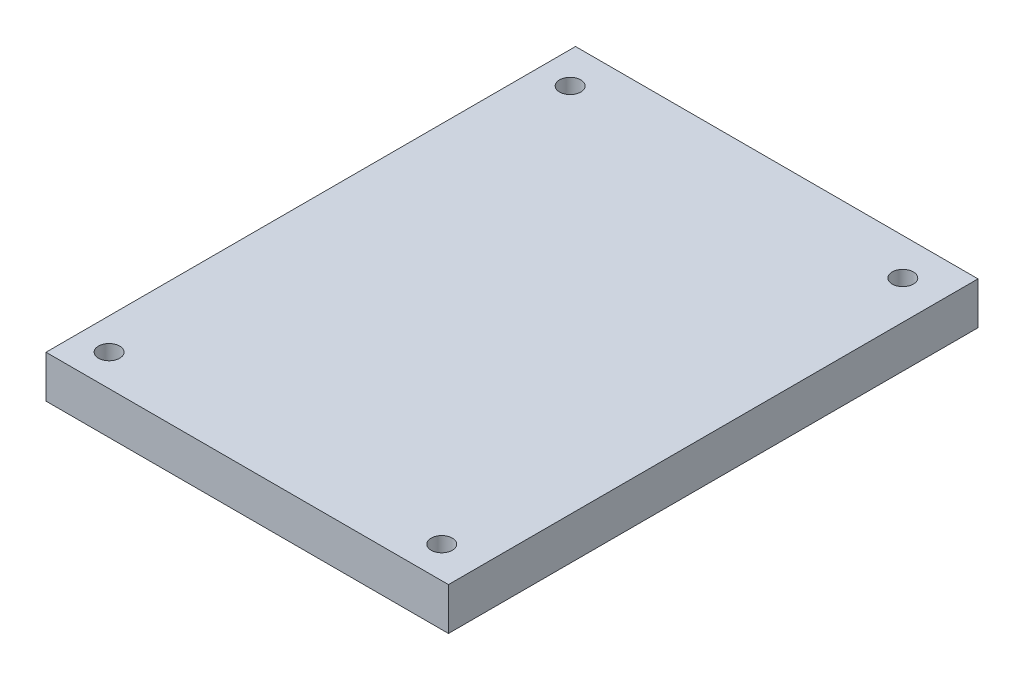
SolidWorks part; units mm, degrees
ref_plane "Ön Düzlem" through (0, 0, 0) normal (0, 0, 1) x (1, 0, 0)
ref_plane "Üst Düzlem" through (0, 0, 0) normal (0, 1, 0) x (1, 0, 0)
ref_plane "Sağ Düzlem" through (0, 0, 0) normal (1, 0, 0) x (0, 0, -1)
sketch "Çizim1" plane through (0, 0, 0) normal (0, 1, 0) x (1, 0, 0)
  line L1 (-7.4468, -9.641) -> (11.5532, -9.641)
  line L2 (-7.4468, -9.641) -> (-7.4468, 15.359)
  line L3 (-7.4468, 15.359) -> (11.5532, 15.359)
  line L4 (11.5532, -9.641) -> (11.5532, 15.359)
  circle A0 centre (-5.9608, 13.6191) radius 0.5
  circle A1 centre (9.7429, 13.6191) radius 0.5
  circle A2 centre (-5.9608, -8.1478) radius 0.5
  circle A3 centre (9.7429, -8.1478) radius 0.5
  dimension "D1" = 25
  dimension "D2" = 19
extrude "Yükseklik-Ekstrüzyon1" add sketch "Çizim1" along normal blind 2
